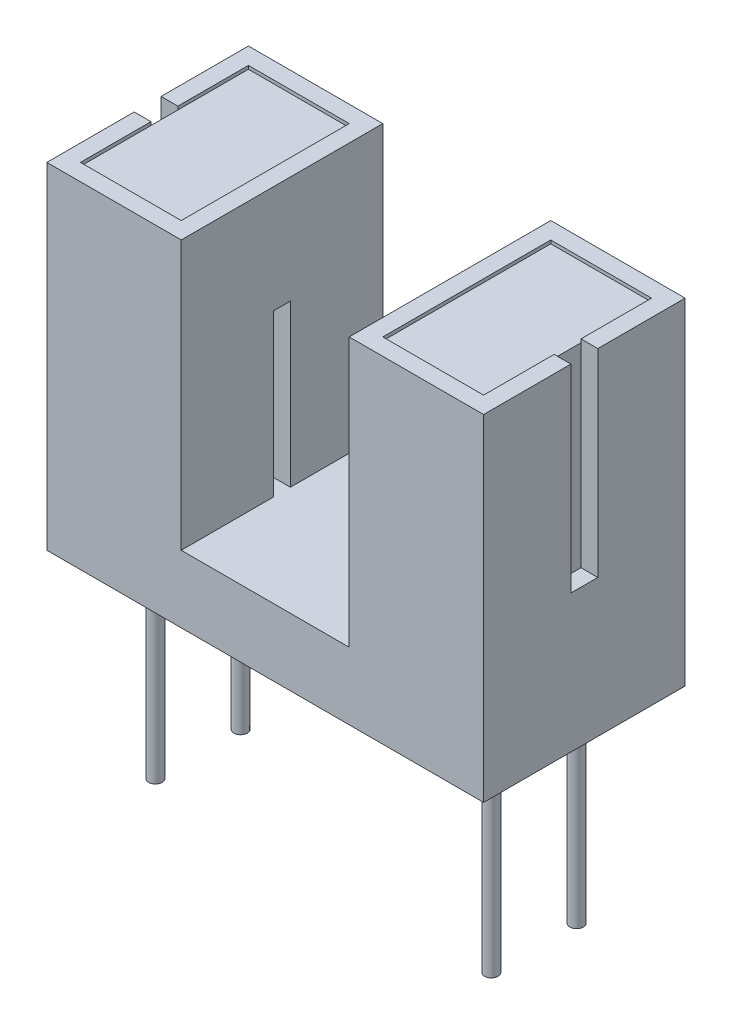
SolidWorks part; units mm, degrees
ref_plane "Plano frontal" through (0, 0, 0) normal (0, 0, 1) x (1, 0, 0)
ref_plane "Plano superior" through (0, 0, 0) normal (0, 1, 0) x (1, 0, 0)
ref_plane "Plano direito" through (0, 0, 0) normal (1, 0, 0) x (0, 0, -1)
sketch "Esboço2" plane through (0, 0, 0) normal (0, 1, 0) x (1, 0, 0)
  line L1 (-6.5, -3) -> (6.5, -3)
  line L2 (-6.5, -3) -> (-6.5, 3)
  line L3 (-6.5, 3) -> (6.5, 3)
  line L4 (6.5, -3) -> (6.5, 3)
  line L5 (-6.5, -3) -> (6.5, 3) construction
  line L6 (-6.5, 3) -> (6.5, -3) construction
  point P0 (0, 0)
  dimension "D1" = 13
  dimension "D2" = 6
extrude "Ressalto-extrusão1" add sketch "Esboço2" along normal blind 10
sketch "Esboço3" plane through (0, 10, 0) normal (0, 1, 0) x (1, 0, 0)
  line L0 (6.5, 3) -> (-6.5, 3) construction
  line L1 (-2.5, -3) -> (2.5, -3)
  line L2 (-2.5, -3) -> (-2.5, 3)
  line L3 (-2.5, 3) -> (2.5, 3)
  line L4 (2.5, -3) -> (2.5, 3)
  line L5 (-2.5, -3) -> (2.5, 3) construction
  line L6 (-2.5, 3) -> (2.5, -3) construction
  point P0 (0, 0)
  dimension "D1" = 5
extrude "Corte-extrusão1" cut sketch "Esboço3" against normal blind 8
sketch "Esboço4" plane through (0, 10, 0) normal (0, 1, 0) x (1, 0, 0)
  line L0 (-6.5, 3) -> (-6.5, -3) construction
  line L1 (-6, -2.5) -> (-3, -2.5)
  line L2 (-6, -2.5) -> (-6, 2.5)
  line L3 (-6, 2.5) -> (-3, 2.5)
  line L4 (-3, -2.5) -> (-3, 2.5)
  line L5 (-6, -2.5) -> (-3, 2.5) construction
  line L6 (-6, 2.5) -> (-3, -2.5) construction
  line L7 (-2.5, 3) -> (-2.5, -3) construction
  line L8 (-2.5, 3) -> (-6.5, 3) construction
  line L9 (-6.5, -3) -> (-2.5, -3) construction
  point P0 (-4.5, 0)
  dimension "D1" = 0.5
  dimension "D2" = 0.5
  dimension "D3" = 0.5
  dimension "D4" = 0.5
extrude "Corte-extrusão2" cut sketch "Esboço4" against normal blind 0.1
mirror "Espelhar1" about plane through (0, 0, 0) normal (1, 0, 0) of "Corte-extrusão2"
sketch "Esboço5" plane through (0, 10, 0) normal (0, 1, 0) x (1, 0, 0)
  line L0 (-6.5, 3) -> (-6.5, -3) construction
  line L1 (-7, -0.4) -> (-6, -0.4)
  line L2 (-7, -0.4) -> (-7, 0.4)
  line L3 (-7, 0.4) -> (-6, 0.4)
  line L4 (-6, -0.4) -> (-6, 0.4)
  line L5 (-7, -0.4) -> (-6, 0.4) construction
  line L6 (-7, 0.4) -> (-6, -0.4) construction
  line L7 (-6, 2.5) -> (-6, -2.5) construction
  point P0 (-6.5, 0)
  dimension "D1" = 0.8
extrude "Corte-extrusão3" cut sketch "Esboço5" against normal blind 5.9
mirror "Espelhar2" about plane through (0, 0, 0) normal (1, 0, 0) of "Corte-extrusão3"
ref_plane "Plano1" through (0, 6.8, 0) normal (0, 1, 0) x (1, 0, 0)
sketch "Esboço6" plane through (0, 6.8, 0) normal (0, 1, 0) x (1, 0, 0)
  line L0 (-2.5, 3) -> (-2.5, -3) construction
  line L1 (-2, -0.25) -> (-3, -0.25)
  line L2 (-2, -0.25) -> (-2, 0.25)
  line L3 (-2, 0.25) -> (-3, 0.25)
  line L4 (-3, -0.25) -> (-3, 0.25)
  line L5 (-2, -0.25) -> (-3, 0.25) construction
  line L6 (-2, 0.25) -> (-3, -0.25) construction
  line L7 (-3, -2.5) -> (-3, 2.5) construction
  point P0 (-2.5, 0)
  dimension "D1" = 0.5
extrude "Corte-extrusão4" cut sketch "Esboço6" against normal up to surface (4.8 mm away) up to face at (0, 2, 0)
mirror "Espelhar3" about plane through (0, 0, 0) normal (1, 0, 0) of "Corte-extrusão4"
sketch "Esboço7" plane through (0, 0, 0) normal (0, -1, 0) x (1, 0, 0)
  line L1 (-5, -1.27) -> (5, -1.27) construction
  line L2 (-5, -1.27) -> (-5, 1.27) construction
  line L3 (-5, 1.27) -> (5, 1.27) construction
  line L4 (5, -1.27) -> (5, 1.27) construction
  line L5 (-5, -1.27) -> (5, 1.27) construction
  line L6 (-5, 1.27) -> (5, -1.27) construction
  circle A0 centre (-5, 1.27) radius 0.2
  circle A1 centre (5, 1.27) radius 0.2
  circle A2 centre (5, -1.27) radius 0.2
  circle A3 centre (-5, -1.27) radius 0.2
  point P0 (0, 0)
  dimension "D3" = 0.4
  dimension "D1" = 10
  dimension "D2" = 2.54
extrude "Ressalto-extrusão2" add sketch "Esboço7" along normal blind 6
